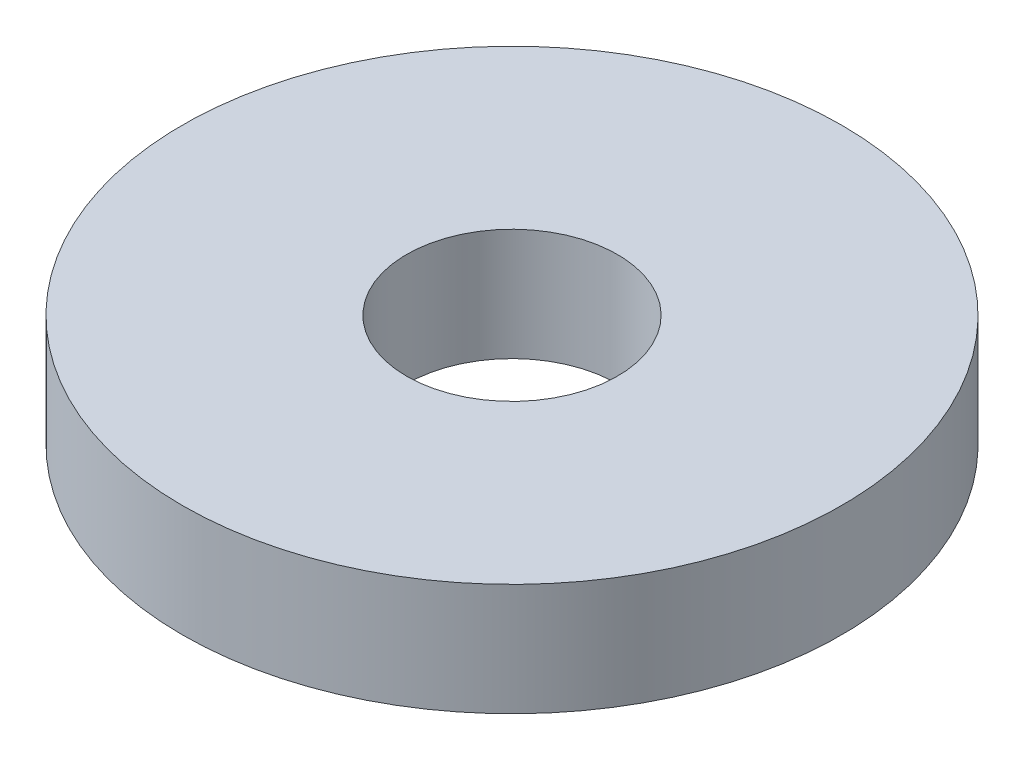
SolidWorks part; units mm, degrees
ref_plane "Front" through (0, 0, 0) normal (0, 0, 1) x (1, 0, 0)
ref_plane "Top" through (0, 0, 0) normal (0, 1, 0) x (1, 0, 0)
ref_plane "Right" through (0, 0, 0) normal (1, 0, 0) x (0, 0, -1)
sketch "Sketch1" plane through (0, 0, 0) normal (0, 1, 0) x (1, 0, 0)
  circle A0 centre (0, 0) radius 5
  circle A1 centre (0, 0) radius 1.6
  dimension "D1" = 10
  dimension "D2" = 3.2
extrude "Boss-Extrude1" add sketch "Sketch1" along normal blind 1.7
